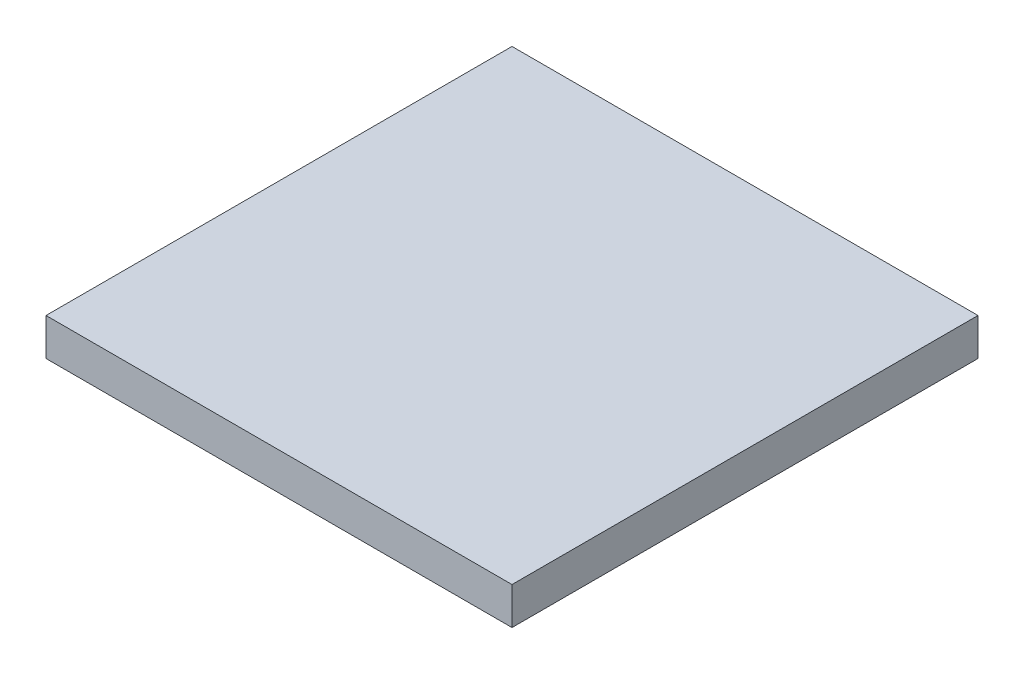
SolidWorks part; units mm, degrees
ref_plane "Front Plane" through (0, 0, 0) normal (0, 0, 1) x (1, 0, 0)
ref_plane "Top Plane" through (0, 0, 0) normal (0, 1, 0) x (1, 0, 0)
ref_plane "Right Plane" through (0, 0, 0) normal (1, 0, 0) x (0, 0, -1)
sketch "Sketch1" plane through (0, 0, 0) normal (0, 1, 0) x (1, 0, 0)
  line L1 (125, 125) -> (-125, 125)
  line L2 (125, 125) -> (125, -125)
  line L3 (125, -125) -> (-125, -125)
  line L4 (-125, 125) -> (-125, -125)
  line L5 (125, 125) -> (-125, -125) construction
  line L6 (125, -125) -> (-125, 125) construction
  point P0 (0, 0)
  point P6 (125, 125)
  dimension "D1" = 250
  dimension "D2" = 250
extrude "Boss-Extrude1" add sketch "Sketch1" along normal blind 20 contours L1 L4 L3 L2
